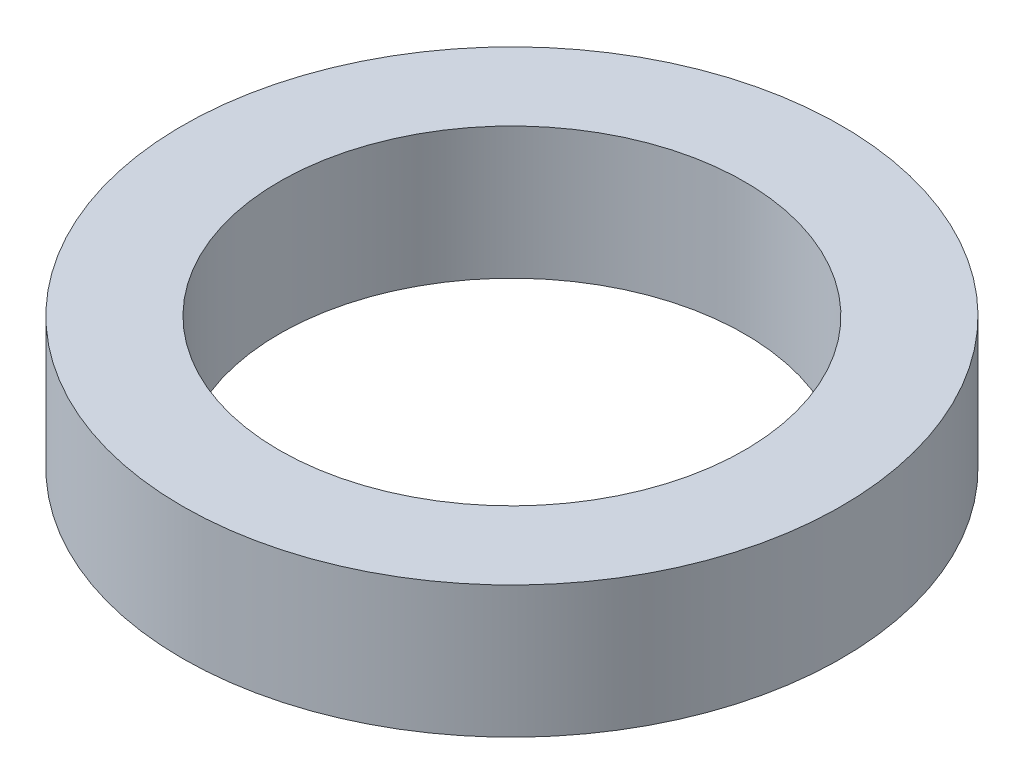
SolidWorks part; units mm, degrees
ref_plane "前视基准面" through (0, 0, 0) normal (0, 0, 1) x (1, 0, 0)
ref_plane "上视基准面" through (0, 0, 0) normal (0, 1, 0) x (1, 0, 0)
ref_plane "右视基准面" through (0, 0, 0) normal (1, 0, 0) x (0, 0, -1)
sketch "草图2" plane through (0, 0, 0) normal (0, 1, 0) x (1, 0, 0)
  circle A0 centre (0, 0) radius 42.5
  circle A1 centre (0, 0) radius 30
  dimension "D1" = 85
  dimension "D2" = 60
extrude "凸台-拉伸1" add sketch "草图2" along normal blind 17
